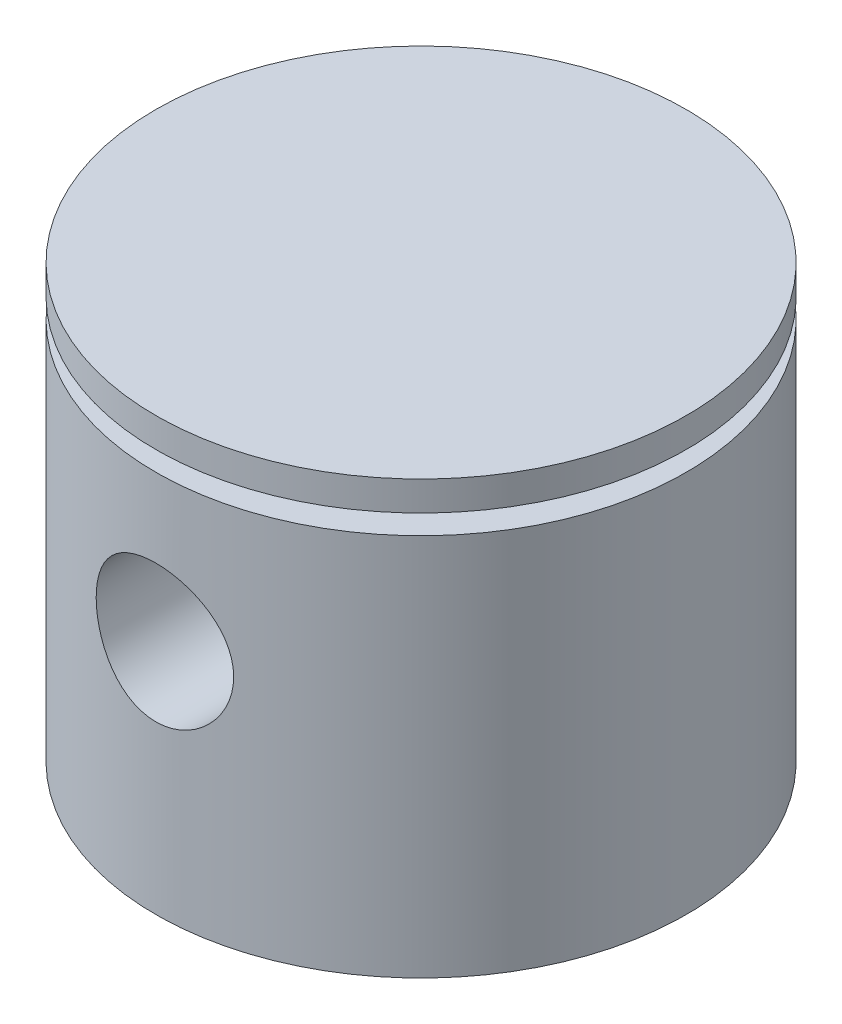
SolidWorks part; units mm, degrees
ref_plane "Plan de face" through (0, 0, 0) normal (0, 0, 1) x (1, 0, 0)
ref_plane "Plan de dessus" through (0, 0, 0) normal (0, 1, 0) x (1, 0, 0)
ref_plane "Plan de droite" through (0, 0, 0) normal (1, 0, 0) x (0, 0, -1)
sketch "Esquisse1" plane through (0, 0, 0) normal (0, 0, 1) x (1, 0, 0)
  line L0 (0, 0) -> (0, -3)
  line L1 (0, -3) -> (-7, -3)
  line L2 (-7, -3) -> (-7, -16)
  line L3 (-7, -16) -> (-12, -16)
  line L4 (-12, -16) -> (-12, -22)
  line L5 (-12, -22) -> (-13.5, -22)
  line L6 (-13.5, -22) -> (-13.5, -2.5)
  line L7 (-13.5, -2.5) -> (-11.5, -2.5)
  line L8 (-11.5, -2.5) -> (-11.5, -1.5)
  line L9 (-11.5, -1.5) -> (-13.5, -1.5)
  line L10 (-13.5, -1.5) -> (-13.5, 0)
  line L11 (-13.5, 0) -> (0, 0)
  dimension "D1" = 13.5
  dimension "D2" = 3
  dimension "D3" = 7
  dimension "D4" = 13
  dimension "D5" = 5
  dimension "D6" = 22
  dimension "D7" = 1
  dimension "D8" = 2
  dimension "D9" = 0.5
  dimension "D10" = 0
revolve "Révolution1" add sketch "Esquisse1" angle 360 about L0
sketch "Esquisse2" plane through (0, 0, 0) normal (0, 0, 1) x (1, 0, 0)
  line L0 (0, 0) -> (0, -22)
  line L1 (-13.5, -22) -> (13.5, -22) construction
  circle A1 centre (0, -10) radius 3.5
  dimension "D2" = 7
  dimension "D1" = 10
extrude "Enlèv. mat.-Extru.1" cut sketch "Esquisse2" against normal through all both and the other way through all contours A1
